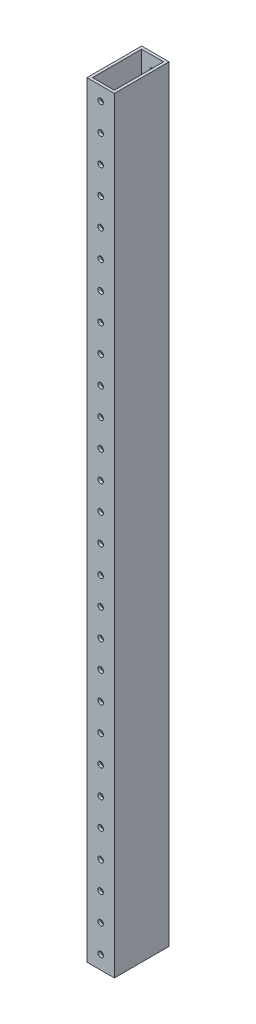
SolidWorks part; units mm, degrees
ref_plane "Front Plane" through (0, 0, 0) normal (0, 0, 1) x (1, 0, 0)
ref_plane "Top Plane" through (0, 0, 0) normal (0, 1, 0) x (1, 0, 0)
ref_plane "Right Plane" through (0, 0, 0) normal (1, 0, 0) x (0, 0, -1)
sketch "Sketch1" plane through (0, 0, 0) normal (0, 1, 0) x (1, 0, 0)
  line L1 (-48.7617, 35.3154) -> (-23.3617, 35.3154)
  line L2 (-48.7617, 35.3154) -> (-48.7617, -15.4846)
  line L3 (-48.7617, -15.4846) -> (-23.3617, -15.4846)
  line L4 (-23.3617, 35.3154) -> (-23.3617, -15.4846)
  line L5 (-46.2217, 32.7754) -> (-25.9017, 32.7754)
  line L6 (-46.2217, 32.7754) -> (-46.2217, -12.9446)
  line L7 (-46.2217, -12.9446) -> (-25.9017, -12.9446)
  line L8 (-25.9017, 32.7754) -> (-25.9017, -12.9446)
  dimension "D1" = 25.4
  dimension "D2" = 50.8
  dimension "D3" = 2.54
  dimension "D4" = 2.54
  dimension "D5" = 2.54
  dimension "D6" = 2.54
extrude "Boss-Extrude2" add sketch "Sketch1" along normal blind 711.2
sketch "Sketch3" plane through (0, 0, 15.4846) normal (0, 0, 1) x (1, 0, 0)
  line L0 (-48.7617, 0) -> (-23.3617, 0) construction
  line L1 (-23.3617, 711.2) -> (-23.3617, 0) construction
  circle A0 centre (-36.0617, 12.7) radius 2.54
  circle A1 centre (-36.0617, 38.1) radius 2.54
  circle A2 centre (-36.0617, 63.5) radius 2.54
  circle A3 centre (-36.0617, 88.9) radius 2.54
  circle A4 centre (-36.0617, 114.3) radius 2.54
  circle A5 centre (-36.0617, 139.7) radius 2.54
  circle A6 centre (-36.0617, 165.1) radius 2.54
  circle A7 centre (-36.0617, 190.5) radius 2.54
  circle A8 centre (-36.0617, 215.9) radius 2.54
  circle A9 centre (-36.0617, 241.3) radius 2.54
  circle A10 centre (-36.0617, 266.7) radius 2.54
  circle A11 centre (-36.0617, 292.1) radius 2.54
  circle A12 centre (-36.0617, 317.5) radius 2.54
  circle A13 centre (-36.0617, 342.9) radius 2.54
  circle A14 centre (-36.0617, 368.3) radius 2.54
  circle A15 centre (-36.0617, 393.7) radius 2.54
  circle A16 centre (-36.0617, 419.1) radius 2.54
  circle A17 centre (-36.0617, 444.5) radius 2.54
  circle A18 centre (-36.0617, 469.9) radius 2.54
  circle A19 centre (-36.0617, 495.3) radius 2.54
  circle A20 centre (-36.0617, 520.7) radius 2.54
  circle A21 centre (-36.0617, 546.1) radius 2.54
  circle A22 centre (-36.0617, 571.5) radius 2.54
  circle A23 centre (-36.0617, 596.9) radius 2.54
  circle A24 centre (-36.0617, 622.3) radius 2.54
  circle A25 centre (-36.0617, 647.7) radius 2.54
  circle A26 centre (-36.0617, 673.1) radius 2.54
  circle A27 centre (-36.0617, 698.5) radius 2.54
  dimension "D1" = 5.08
  dimension "D2" = 12.7
  dimension "D4" = 28
  dimension "D3" = 12.7
extrude "Cut-Extrude1" cut sketch "Sketch3" against normal through all and the other way through all
